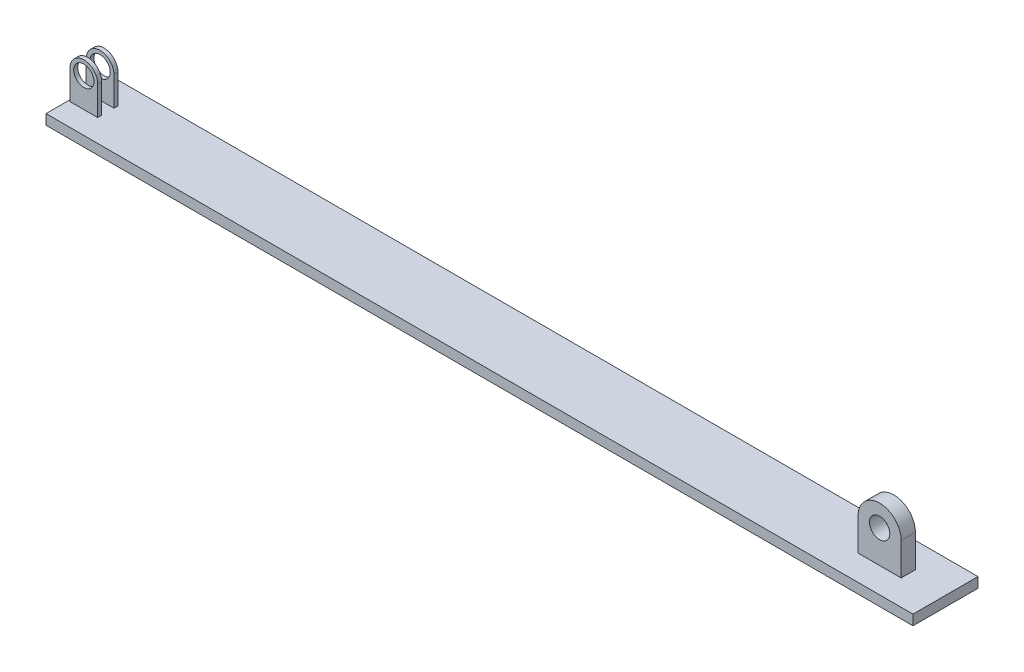
SolidWorks part; units mm, degrees
material "6061 Alloy"
ref_plane "Front Plane" through (0, 0, 0) normal (0, 0, 1) x (1, 0, 0)
ref_plane "Top Plane" through (0, 0, 0) normal (0, 1, 0) x (1, 0, 0)
ref_plane "Right Plane" through (0, 0, 0) normal (1, 0, 0) x (0, 0, -1)
sketch "Sketch1" plane through (0, 0, 0) normal (0, 0, -1) x (1, 0, 0)
  line L0 (0, -55) -> (0, 55) construction
  line L1 (0, 2.5) -> (426.72, 2.5)
  line L2 (0, 2.5) -> (0, -2.5)
  line L3 (0, -2.5) -> (426.72, -2.5)
  line L4 (426.72, 2.5) -> (426.72, -2.5)
  line L5 (426.72, 0) -> (0, 0) construction
  dimension "D1" = 5
  dimension "D2" = 426.72
extrude "Extrude2" add sketch "Sketch1" along normal mid plane 32
sketch "Sketch2" plane through (0, 0, 0) normal (0, 0, 1) x (1, 0, 0)
  line L0 (7.6165, 2.5) -> (7.6165, 11.837) construction
  line L1 (0, 2.5) -> (426.72, 2.5) construction
  line L2 (0.8031, 2.5) -> (0.8031, 16.9215)
  line L3 (14.4299, 2.5) -> (14.4299, 16.9215)
  line L4 (0.8031, 2.5) -> (14.4299, 2.5)
  arc A0 (0.8031, 16.9215) -> (14.4299, 16.9215) centre (7.6165, 16.9215) cw
  circle A1 centre (7.6165, 16.9215) radius 5
  dimension "D1" = 10
extrude "Extrude3" add sketch "Sketch2" along normal mid plane 10
sketch "Sketch3" plane through (0.8031, 0, 0) normal (-1, 0, 0) x (0, 0, 1)
  line L0 (-16, 2.5) -> (16, 2.5) construction
  line L1 (-3, 2.5) -> (3, 2.5)
  line L2 (-3, 2.5) -> (-3, 43.4954)
  line L3 (-3, 43.4954) -> (3, 43.4954)
  line L4 (3, 2.5) -> (3, 43.4954)
  line L5 (0, 43.4954) -> (0, 2.5) construction
  line L6 (0, -14.4292) -> (0, 14.4292) construction
  dimension "D1" = 6
extrude "Cut-Extrude1" cut sketch "Sketch3" against normal up to surface (13.6268 mm away) up to face at (14.4299, 9.7108, 0)
sketch "Sketch4" plane through (0, 0, 0) normal (0, 0, 1) x (1, 0, 0)
  line L0 (397.8057, 2.5) -> (397.8057, 18.5157) construction
  line L1 (0, 2.5) -> (426.72, 2.5) construction
  line L2 (408.3986, 2.5) -> (408.3986, 18.5157)
  line L3 (387.2127, 2.5) -> (387.2127, 18.5157)
  line L4 (387.2127, 2.5) -> (408.3986, 2.5)
  arc A0 (408.3986, 18.5157) -> (387.2127, 18.5157) centre (397.8057, 18.5157) ccw
  circle A1 centre (397.8057, 18.5157) radius 5
  dimension "D1" = 10
extrude "Extrude4" add sketch "Sketch4" along normal mid plane 7
